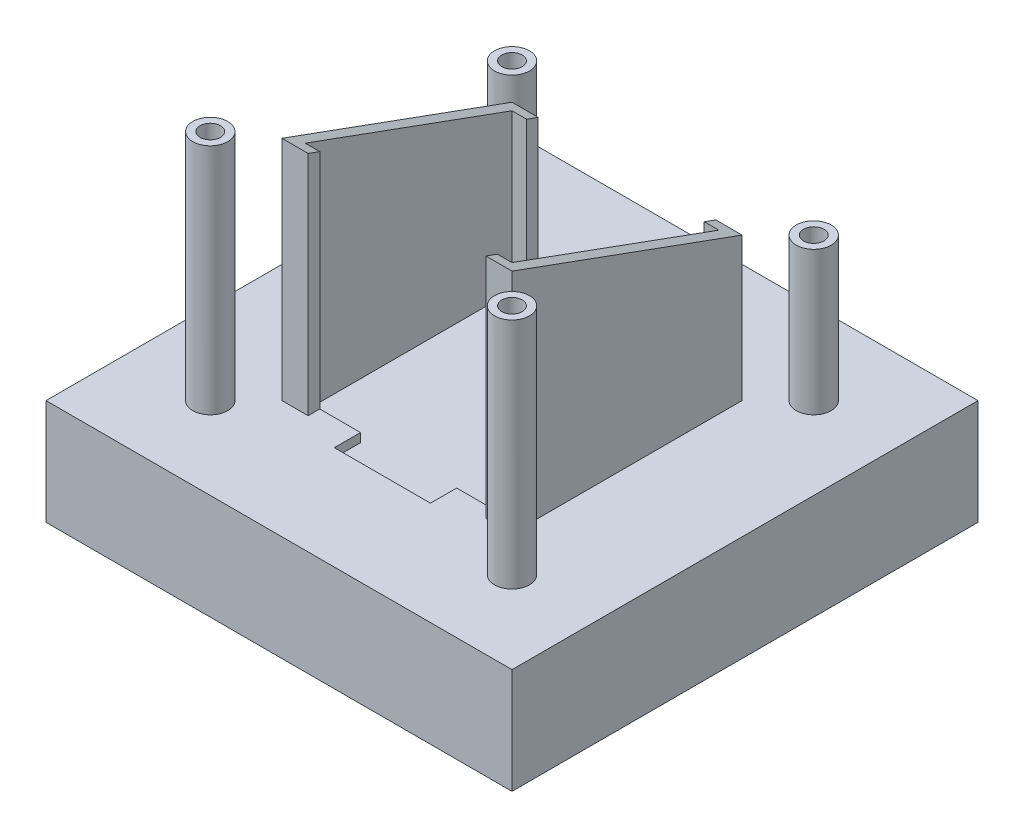
SolidWorks part; units mm, degrees
ref_plane "Front Plane" through (0, 0, 0) normal (0, 0, 1) x (1, 0, 0)
ref_plane "Top Plane" through (0, 0, 0) normal (0, 1, 0) x (1, 0, 0)
ref_plane "Right Plane" through (0, 0, 0) normal (1, 0, 0) x (0, 0, -1)
sketch "Sketch1" plane through (0, 0, 0) normal (0, 1, 0) x (1, 0, 0)
  line L1 (-40, -40) -> (40, -40)
  line L2 (-40, -40) -> (-40, 40)
  line L3 (-40, 40) -> (40, 40)
  line L4 (40, -40) -> (40, 40)
  line L5 (-40, -40) -> (40, 40) construction
  line L6 (-40, 40) -> (40, -40) construction
  point P0 (0, 0)
  dimension "D1" = 80
  dimension "D2" = 80
extrude "Boss-Extrude1" add sketch "Sketch1" along normal blind 4
sketch "Sketch2" plane through (0, 4, 0) normal (0, 1, 0) x (1, 0, 0)
  line L0 (8.25, -17.75) -> (17.75, -17.75)
  line L1 (-17.75, -17.75) -> (-8.25, -17.75)
  line L2 (-17.75, -17.75) -> (-17.75, 17.75)
  line L3 (-17.75, 17.75) -> (17.75, 17.75)
  line L4 (17.75, -17.75) -> (17.75, 17.75)
  line L5 (-17.75, -17.75) -> (17.75, 17.75) construction
  line L6 (-17.75, 17.75) -> (17.75, -17.75) construction
  line L7 (-8.25, -22.25) -> (8.25, -22.25)
  line L8 (-8.25, -22.25) -> (-8.25, -17.75)
  line L10 (8.25, -22.25) -> (8.25, -17.75)
  line L11 (-8.25, -22.25) -> (8.25, -17.75) construction
  line L12 (-8.25, -17.75) -> (8.25, -22.25) construction
  point P0 (0, 0)
  point P6 (0, -20)
  dimension "D1" = 35.5
  dimension "D2" = 35.5
  dimension "D3" = 4.5
  dimension "D4" = 16.5
extrude "Cut-Extrude1" cut sketch "Sketch2" against normal blind 1.5 contours L8 L1 L2 L3 L4 L0 L10 L7
sketch "Sketch3" plane through (0, 4, 0) normal (0, 1, 0) x (1, 0, 0)
  line L0 (-19.75, 17.75) -> (-19.75, -17.75)
  line L1 (19.75, 17.75) -> (19.75, -17.75)
  line L2 (17.75, 19.75) -> (19.75, 19.75)
  line L3 (19.75, 19.75) -> (19.75, 17.75)
  line L4 (19.75, -17.75) -> (19.75, -19.75)
  line L5 (8.25, -17.75) -> (17.75, -17.75) construction
  line L6 (17.75, -19.75) -> (15.25, -19.75)
  line L7 (-17.75, 17.75) -> (-17.75, -17.75)
  line L8 (19.75, -19.75) -> (17.75, -19.75)
  line L9 (-19.75, -17.75) -> (-19.75, -19.75)
  line L10 (17.75, -17.75) -> (15.25, -17.75)
  line L11 (17.75, -17.75) -> (17.75, 17.75)
  line L12 (15.25, -19.75) -> (15.25, -17.75)
  line L13 (-17.75, 17.75) -> (17.75, 17.75) construction
  line L14 (17.75, 19.75) -> (15.25, 19.75)
  line L15 (-19.75, -19.75) -> (-17.75, -19.75)
  line L16 (17.75, 17.75) -> (15.25, 17.75)
  line L17 (15.25, 19.75) -> (15.25, 17.75)
  line L18 (-17.75, 19.75) -> (-15.25, 19.75)
  line L19 (-17.75, 19.75) -> (-19.75, 19.75)
  line L20 (-17.75, 17.75) -> (-15.25, 17.75)
  line L21 (-15.25, 19.75) -> (-15.25, 17.75)
  line L22 (-17.75, -17.75) -> (-8.25, -17.75) construction
  line L23 (-17.75, -19.75) -> (-15.25, -19.75)
  line L24 (-19.75, 19.75) -> (-19.75, 17.75)
  line L25 (-17.75, -17.75) -> (-15.25, -17.75)
  line L26 (-15.25, -19.75) -> (-15.25, -17.75)
extrude "Boss-Extrude2" add sketch "Sketch3" along normal blind 39
sketch "Sketch5" plane through (0, 4, 0) normal (0, 1, 0) x (1, 0, 0)
  line L0 (0, -47.7081) -> (0, 58.4275) construction
  line L1 (58.7758, 0) -> (-60.5822, 0) construction
  circle A0 centre (25.9, 25.9) radius 1.75
  circle A1 centre (25.9, 25.9) radius 3
  circle A2 centre (-25.9, 25.9) radius 1.75
  circle A3 centre (-25.9, 25.9) radius 3
  circle A4 centre (-25.9, -25.9) radius 1.75
  circle A5 centre (-25.9, -25.9) radius 3
  circle A6 centre (25.9, -25.9) radius 1.75
  circle A7 centre (25.9, -25.9) radius 3
  dimension "D1" = 3.5
  dimension "D2" = 6
  dimension "D3" = 3.5
  dimension "D4" = 6
  dimension "D5" = 3.5
  dimension "D6" = 6
  dimension "D7" = 3.5
  dimension "D8" = 6
  dimension "D9" = 51.8
  dimension "D10" = 51.8
  dimension "D11" = 51.8
  dimension "D12" = 25.9
  dimension "D13" = 51.8
  dimension "D14" = 25.9
  dimension "D15" = 25.9
  dimension "D16" = 25.9
extrude "Boss-Extrude3" add sketch "Sketch5" along normal blind 40
sketch "Sketch6" plane through (0, 44, 0) normal (0, 1, 0) x (1, 0, 0)
  circle A0 centre (-25.9, 25.9) radius 4.5
  circle A1 centre (25.9, 25.9) radius 4.5
extrude "Cut-Extrude2" cut sketch "Sketch6" against normal blind 15.39
sketch "Sketch7" plane through (-19.75, 0, 0) normal (-1, 0, 0) x (0, 0, 1)
  line L0 (-28.9, 28.61) -> (47.1028, 28.61) construction
  line L1 (28.9, 44) -> (-42.1565, 44) construction
  line L2 (-19.75, 28.61) -> (19.75, 43)
  line L3 (-19.75, 43) -> (-19.75, 4) construction
  line L4 (-19.75, 28.61) -> (-19.75, 43)
  line L5 (-19.75, 43) -> (19.75, 43)
extrude "Cut-Extrude3" cut sketch "Sketch7" against normal through all
sketch "Sketch9" plane through (0, 4, 0) normal (0, 1, 0) x (1, 0, 0)
  circle A0 centre (-25.9, 25.9) radius 1.75
  circle A1 centre (-25.9, -25.9) radius 1.75
  circle A2 centre (25.9, -25.9) radius 1.75
  circle A3 centre (25.9, 25.9) radius 1.75
  dimension "D1" = 3.5
  dimension "D2" = 3.5
  dimension "D3" = 3.5
  dimension "D4" = 3.5
extrude "Cut-Extrude4" cut sketch "Sketch9" against normal through all both and the other way through all
sketch "Sketch10" plane through (0, 0, 0) normal (0, -1, 0) x (1, 0, 0)
  line L1 (40, -40) -> (-40, -40)
  line L2 (40, -40) -> (40, 40)
  line L3 (40, 40) -> (-40, 40)
  line L4 (-40, -40) -> (-40, 40)
  line L5 (36, -36) -> (-36, -36)
  line L6 (36, -36) -> (36, 36)
  line L7 (36, 36) -> (-36, 36)
  line L8 (-36, -36) -> (-36, 36)
  dimension "D1" = 4
  dimension "D2" = 4
  dimension "D3" = 4
  dimension "D4" = 4
extrude "Boss-Extrude5" add sketch "Sketch10" along normal blind 14.1
